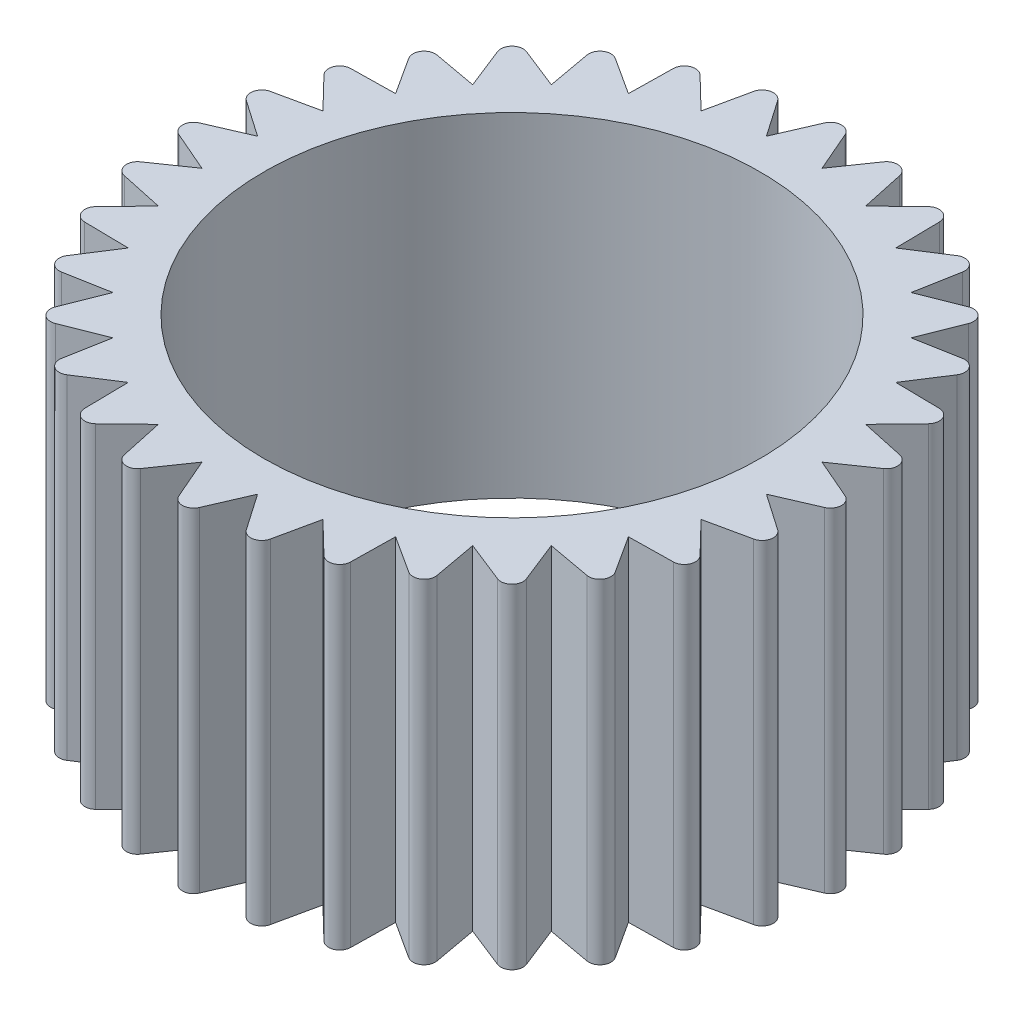
SolidWorks part; units mm, degrees
ref_plane "Front Plane" through (0, 0, 0) normal (0, 0, 1) x (1, 0, 0)
ref_plane "Top Plane" through (0, 0, 0) normal (0, 1, 0) x (1, 0, 0)
ref_plane "Right Plane" through (0, 0, 0) normal (1, 0, 0) x (0, 0, -1)
sketch "Sketch1" plane through (0, 0, 0) normal (0, 1, 0) x (1, 0, 0)
  line L1 (0, -55) -> (0, 55) construction
  line L2 (0, 15.5596) -> (-1.2485, 12.6766)
  line L3 (-1.2485, 12.6766) -> (0, 15.5596)
  line L4 (0, 15.5596) -> (1.2485, 12.6766)
  line L7 (3.0355, 15.2606) -> (1.2485, 12.6766)
  line L8 (3.0355, 15.2606) -> (3.6976, 12.1895)
  line L10 (5.9544, 14.3752) -> (3.6976, 12.1895)
  line L11 (5.9544, 14.3752) -> (6.0046, 11.2339)
  line L13 (8.6444, 12.9373) -> (6.0046, 11.2339)
  line L14 (8.6444, 12.9373) -> (8.0809, 9.8466)
  line L16 (11.0023, 11.0023) -> (8.0809, 9.8466)
  line L17 (11.0023, 11.0023) -> (9.8466, 8.0809)
  line L19 (12.9373, 8.6444) -> (9.8466, 8.0809)
  line L20 (12.9373, 8.6444) -> (11.2339, 6.0046)
  line L22 (14.3752, 5.9544) -> (11.2339, 6.0046)
  line L23 (14.3752, 5.9544) -> (12.1895, 3.6976)
  line L25 (15.2606, 3.0355) -> (12.1895, 3.6976)
  line L26 (15.2606, 3.0355) -> (12.6766, 1.2485)
  line L28 (15.5596, 0) -> (12.6766, 1.2485)
  line L29 (15.5596, 0) -> (12.6766, -1.2485)
  line L31 (15.2606, -3.0355) -> (12.6766, -1.2485)
  line L32 (15.2606, -3.0355) -> (12.1895, -3.6976)
  line L34 (14.3752, -5.9544) -> (12.1895, -3.6976)
  line L35 (14.3752, -5.9544) -> (11.2339, -6.0046)
  line L37 (12.9373, -8.6444) -> (11.2339, -6.0046)
  line L38 (12.9373, -8.6444) -> (9.8466, -8.0809)
  line L40 (11.0023, -11.0023) -> (9.8466, -8.0809)
  line L41 (11.0023, -11.0023) -> (8.0809, -9.8466)
  line L43 (8.6444, -12.9373) -> (8.0809, -9.8466)
  line L44 (8.6444, -12.9373) -> (6.0046, -11.2339)
  line L46 (5.9544, -14.3752) -> (6.0046, -11.2339)
  line L47 (5.9544, -14.3752) -> (3.6976, -12.1895)
  line L49 (3.0355, -15.2606) -> (3.6976, -12.1895)
  line L50 (3.0355, -15.2606) -> (1.2485, -12.6766)
  line L52 (0, -15.5596) -> (1.2485, -12.6766)
  line L53 (0, -15.5596) -> (-1.2485, -12.6766)
  line L55 (-3.0355, -15.2606) -> (-1.2485, -12.6766)
  line L56 (-3.0355, -15.2606) -> (-3.6976, -12.1895)
  line L58 (-5.9544, -14.3752) -> (-3.6976, -12.1895)
  line L59 (-5.9544, -14.3752) -> (-6.0046, -11.2339)
  line L61 (-8.6444, -12.9373) -> (-6.0046, -11.2339)
  line L62 (-8.6444, -12.9373) -> (-8.0809, -9.8466)
  line L64 (-11.0023, -11.0023) -> (-8.0809, -9.8466)
  line L65 (-11.0023, -11.0023) -> (-9.8466, -8.0809)
  line L67 (-12.9373, -8.6444) -> (-9.8466, -8.0809)
  line L68 (-12.9373, -8.6444) -> (-11.2339, -6.0046)
  line L70 (-14.3752, -5.9544) -> (-11.2339, -6.0046)
  line L71 (-14.3752, -5.9544) -> (-12.1895, -3.6976)
  line L73 (-15.2606, -3.0355) -> (-12.1895, -3.6976)
  line L74 (-15.2606, -3.0355) -> (-12.6766, -1.2485)
  line L76 (-15.5596, 0) -> (-12.6766, -1.2485)
  line L77 (-15.5596, 0) -> (-12.6766, 1.2485)
  line L79 (-15.2606, 3.0355) -> (-12.6766, 1.2485)
  line L80 (-15.2606, 3.0355) -> (-12.1895, 3.6976)
  line L82 (-14.3752, 5.9544) -> (-12.1895, 3.6976)
  line L83 (-14.3752, 5.9544) -> (-11.2339, 6.0046)
  line L85 (-12.9373, 8.6444) -> (-11.2339, 6.0046)
  line L86 (-12.9373, 8.6444) -> (-9.8466, 8.0809)
  line L88 (-11.0023, 11.0023) -> (-9.8466, 8.0809)
  line L89 (-11.0023, 11.0023) -> (-8.0809, 9.8466)
  line L91 (-8.6444, 12.9373) -> (-8.0809, 9.8466)
  line L92 (-8.6444, 12.9373) -> (-6.0046, 11.2339)
  line L94 (-5.9544, 14.3752) -> (-6.0046, 11.2339)
  line L95 (-5.9544, 14.3752) -> (-3.6976, 12.1895)
  line L97 (-3.0355, 15.2606) -> (-3.6976, 12.1895)
  line L98 (-3.0355, 15.2606) -> (-1.2485, 12.6766)
  circle A0 centre (0, 0) radius 11.15
  point P105 (0, 0)
  dimension "D1" = 22.3
  dimension "D2" = 32
extrude "Boss-Extrude1" add sketch "Sketch1" along normal blind 15 contours L98 L97 L95 L94 L92 L91 L89 L88 L86 L85 L83 L82 L80 L79 L77 L76 L74 L73 L71 L70 L68 L67 L65 L64 L62 L61 L59 L58 L56 L55 L53 L52 L50 L49 L47 L46 L44 L43 L41 L40 L38 L37 L35 L34 L32 L31 L29 L28 L26 L25 L23
fillet "Fillet1" radius 0.5 32 edges at (-15.5596, 7.5, 0) (-15.2606, 7.5, -3.0355) (-14.3752, 7.5, -5.9544) (-12.9373, 7.5, -8.6444) (-11.0023, 7.5, -11.0023) (-8.6444, 7.5, -12.9373) (-5.9544, 7.5, -14.3752) (-3.0355, 7.5, -15.2606) (0, 7.5, -15.5596) (3.0355, 7.5, -15.2606) (5.9544, 7.5, -14.3752) (8.6444, 7.5, -12.9373) (11.0023, 7.5, -11.0023) (12.9373, 7.5, -8.6444) (14.3752, 7.5, -5.9544) (15.2606, 7.5, -3.0355) (15.5596, 7.5, 0) (15.2606, 7.5, 3.0355) (14.3752, 7.5, 5.9544) (12.9373, 7.5, 8.6444) (11.0023, 7.5, 11.0023) (8.6444, 7.5, 12.9373) (5.9544, 7.5, 14.3752) (3.0355, 7.5, 15.2606) (0, 7.5, 15.5596) (-3.0355, 7.5, 15.2606) (-5.9544, 7.5, 14.3752) (-8.6444, 7.5, 12.9373) (-11.0023, 7.5, 11.0023) (-12.9373, 7.5, 8.6444) (-14.3752, 7.5, 5.9544) (-15.2606, 7.5, 3.0355)
